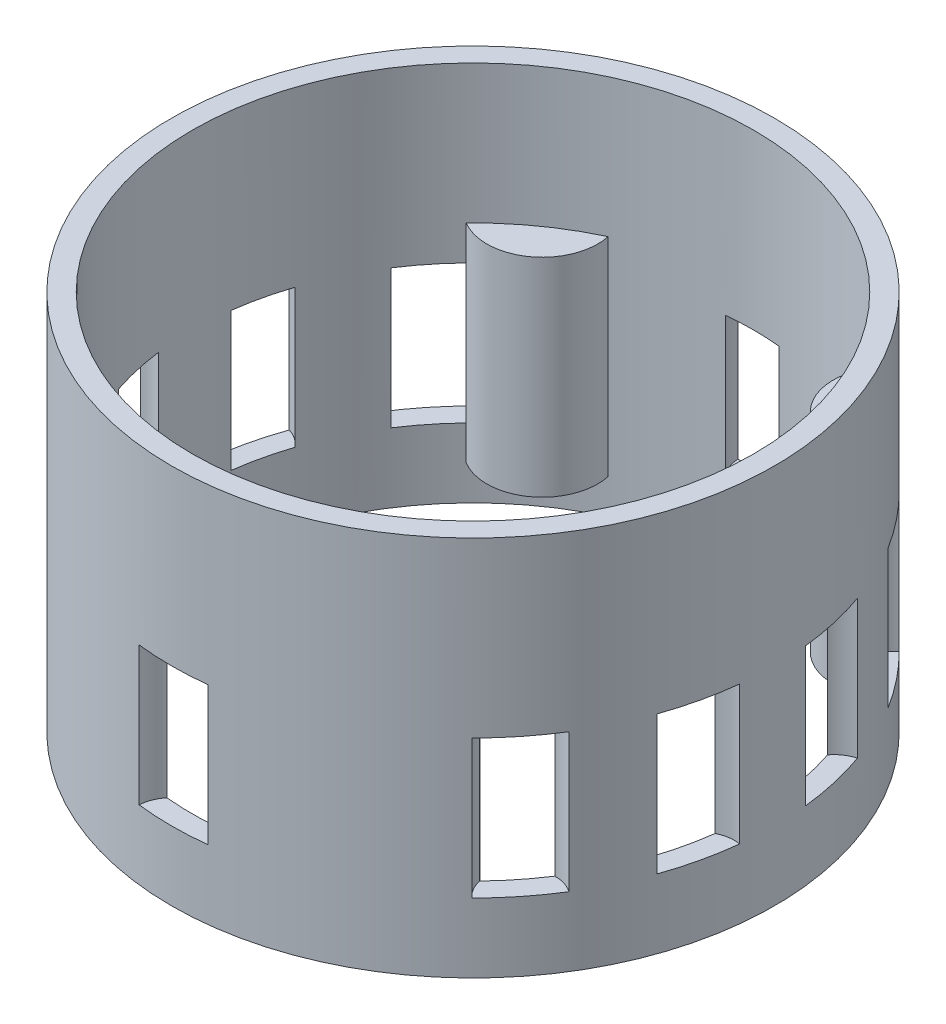
SolidWorks part; units mm, degrees
ref_plane "Front Plane" through (0, 0, 0) normal (0, 0, 1) x (1, 0, 0)
ref_plane "Top Plane" through (0, 0, 0) normal (0, 1, 0) x (1, 0, 0)
ref_plane "Right Plane" through (0, 0, 0) normal (1, 0, 0) x (0, 0, -1)
sketch "Sketch1" plane through (0, 0, 0) normal (0, 1, 0) x (1, 0, 0)
  line L1 (-25, 35) -> (25, 35) construction
  line L2 (-25, 35) -> (-25, -35) construction
  line L3 (-25, -35) -> (25, -35) construction
  line L4 (25, 35) -> (25, -35) construction
  line L5 (-25, 35) -> (25, -35) construction
  line L6 (-25, -35) -> (25, 35) construction
  circle A0 centre (0, 0) radius 40.5
  circle A1 centre (0, 0) radius 43.5
  arc A2 (-29.123, 28.1443) -> (-17.1777, 36.6767) centre (-25, 35) ccw
  arc A3 (17.1777, 36.6767) -> (29.123, 28.1443) centre (25, 35) ccw
  arc A4 (29.123, -28.1443) -> (17.1777, -36.6767) centre (25, -35) ccw
  arc A5 (-17.1777, -36.6767) -> (-29.123, -28.1443) centre (-25, -35) ccw
  dimension "D1" = 81
  dimension "D2" = 87
  dimension "D5" = 16
  dimension "D3" = 70
  dimension "D4" = 50
extrude "Boss-Extrude1" add sketch "Sketch1" along normal blind 30 contours A1 A0 | A0 A2 | A0 A5 | A0 A4 | A0 A3
sketch "Sketch2" plane through (0, 30, 0) normal (0, 1, 0) x (1, 0, 0)
  circle A0 centre (0, 0) radius 43.5
  circle A1 centre (0, 0) radius 40.5
extrude "Boss-Extrude2" add sketch "Sketch2" along normal blind 20
sketch "Sketch3" plane through (0, 0, 0) normal (0, -1, 0) x (1, 0, 0)
  circle A0 centre (0, 0) radius 43.5
  circle A1 centre (0, 0) radius 40.5
extrude "Boss-Extrude3" add sketch "Sketch3" along normal blind 5
ref_plane "Plane1" through (0, 15, 0) normal (0, 1, 0) x (1, 0, 0)
sketch "Sketch4" plane through (0, 0, 0) normal (0, 1, 0) x (1, 0, 0)
  line L0 (0, 0) -> (3.8552, 40.3161) construction
  line L1 (0, 0) -> (20.9659, 34.6508) construction
  circle A0 centre (0, 0) radius 40.5 construction
  circle A1 centre (0, 0) radius 43.5 construction
  arc A2 (3.8552, 40.3161) -> (-3.8552, 40.3161) centre (0, 0) ccw
  arc A3 (4.9917, 43.2126) -> (-4.9917, 43.2126) centre (0, 0) ccw
  arc A4 (3.8552, 40.3161) -> (4.9917, 43.2126) centre (0, 43.5) ccw
  arc A5 (-4.9917, 43.2126) -> (-3.8552, 40.3161) centre (0, 43.5) ccw
  arc A10 (33.9241, 22.1225) -> (29.1167, 28.1508) centre (0, 0) ccw
  arc A11 (30.6727, 30.8453) -> (29.1167, 28.1508) centre (34.0097, 27.1218) ccw
  arc A12 (36.8973, 23.0399) -> (30.6727, 30.8453) centre (0, 0) ccw
  arc A13 (33.9241, 22.1225) -> (36.8973, 23.0399) centre (34.0097, 27.1218) ccw
  arc A14 (40.1632, 5.2126) -> (38.4474, 12.7297) centre (0, 0) ccw
  arc A15 (41.0184, 14.4823) -> (38.4474, 12.7297) centre (42.4094, 9.6797) ccw
  arc A16 (43.24, 4.7491) -> (41.0184, 14.4823) centre (0, 0) ccw
  arc A17 (40.1632, 5.2126) -> (43.24, 4.7491) centre (42.4094, 9.6797) ccw
  arc A18 (38.4474, -12.7297) -> (40.1632, -5.2126) centre (0, 0) ccw
  arc A19 (43.24, -4.7491) -> (40.1632, -5.2126) centre (42.4094, -9.6797) ccw
  arc A20 (41.0184, -14.4823) -> (43.24, -4.7491) centre (0, 0) ccw
  arc A21 (38.4474, -12.7297) -> (41.0184, -14.4823) centre (42.4094, -9.6797) ccw
  arc A22 (29.1167, -28.1508) -> (33.9241, -22.1225) centre (0, 0) ccw
  arc A23 (36.8973, -23.0399) -> (33.9241, -22.1225) centre (34.0097, -27.1218) ccw
  arc A24 (30.6727, -30.8453) -> (36.8973, -23.0399) centre (0, 0) ccw
  arc A25 (29.1167, -28.1508) -> (30.6727, -30.8453) centre (34.0097, -27.1218) ccw
  arc A30 (-3.8552, -40.3161) -> (3.8552, -40.3161) centre (0, 0) ccw
  arc A31 (4.9917, -43.2126) -> (3.8552, -40.3161) centre (0, -43.5) ccw
  arc A32 (-4.9917, -43.2126) -> (4.9917, -43.2126) centre (0, 0) ccw
  arc A33 (-3.8552, -40.3161) -> (-4.9917, -43.2126) centre (0, -43.5) ccw
  arc A38 (-33.9241, -22.1225) -> (-29.1167, -28.1508) centre (0, 0) ccw
  arc A39 (-30.6727, -30.8453) -> (-29.1167, -28.1508) centre (-34.0097, -27.1218) ccw
  arc A40 (-36.8973, -23.0399) -> (-30.6727, -30.8453) centre (0, 0) ccw
  arc A41 (-33.9241, -22.1225) -> (-36.8973, -23.0399) centre (-34.0097, -27.1218) ccw
  arc A42 (-40.1632, -5.2126) -> (-38.4474, -12.7297) centre (0, 0) ccw
  arc A43 (-41.0184, -14.4823) -> (-38.4474, -12.7297) centre (-42.4094, -9.6797) ccw
  arc A44 (-43.24, -4.7491) -> (-41.0184, -14.4823) centre (0, 0) ccw
  arc A45 (-40.1632, -5.2126) -> (-43.24, -4.7491) centre (-42.4094, -9.6797) ccw
  arc A46 (-38.4474, 12.7297) -> (-40.1632, 5.2126) centre (0, 0) ccw
  arc A47 (-43.24, 4.7491) -> (-40.1632, 5.2126) centre (-42.4094, 9.6797) ccw
  arc A48 (-41.0184, 14.4823) -> (-43.24, 4.7491) centre (0, 0) ccw
  arc A49 (-38.4474, 12.7297) -> (-41.0184, 14.4823) centre (-42.4094, 9.6797) ccw
  arc A50 (-29.1167, 28.1508) -> (-33.9241, 22.1225) centre (0, 0) ccw
  arc A51 (-36.8973, 23.0399) -> (-33.9241, 22.1225) centre (-34.0097, 27.1218) ccw
  arc A52 (-30.6727, 30.8453) -> (-36.8973, 23.0399) centre (0, 0) ccw
  arc A53 (-29.1167, 28.1508) -> (-30.6727, 30.8453) centre (-34.0097, 27.1218) ccw
  arc A58 (-14.0191, 37.9963) -> (-14.2519, 41.0991) centre (-18.8739, 39.1921) ccw
  arc A59 (-23.2467, 36.7674) -> (-20.9659, 34.6508) centre (-18.8739, 39.1921) ccw
  arc A60 (-14.2519, 41.0991) -> (-23.2467, 36.7674) centre (0, 0) ccw
  arc A61 (-14.0191, 37.9963) -> (-20.9659, 34.6508) centre (0, 0) ccw
  arc A62 (20.9659, 34.6508) -> (14.0191, 37.9963) centre (0, 0) ccw
  arc A63 (23.2467, 36.7674) -> (14.2519, 41.0991) centre (0, 0) ccw
  arc A64 (14.2519, 41.0991) -> (14.0191, 37.9963) centre (18.8739, 39.1921) ccw
  arc A65 (20.9659, 34.6508) -> (23.2467, 36.7674) centre (18.8739, 39.1921) ccw
  arc A66 (23.2467, -36.7674) -> (20.9659, -34.6508) centre (18.8739, -39.1921) ccw
  arc A67 (14.0191, -37.9963) -> (20.9659, -34.6508) centre (0, 0) ccw
  arc A68 (14.0191, -37.9963) -> (14.2519, -41.0991) centre (18.8739, -39.1921) ccw
  arc A69 (14.2519, -41.0991) -> (23.2467, -36.7674) centre (0, 0) ccw
  arc A70 (-20.9659, -34.6508) -> (-23.2467, -36.7674) centre (-18.8739, -39.1921) ccw
  arc A71 (-14.2519, -41.0991) -> (-14.0191, -37.9963) centre (-18.8739, -39.1921) ccw
  arc A72 (-20.9659, -34.6508) -> (-14.0191, -37.9963) centre (0, 0) ccw
  arc A73 (-23.2467, -36.7674) -> (-14.2519, -41.0991) centre (0, 0) ccw
  dimension "D1" = 10
  dimension "D3" = 25.714
  dimension "D2" = 14
sketch "Sketch5" plane through (0, 15, 0) normal (0, 1, 0) x (1, 0, 0)
  arc A0 (-4.9917, 43.2126) -> (-3.8552, 40.3161) centre (0, 43.5) ccw construction
  arc A1 (4.9917, 43.2126) -> (-4.9917, 43.2126) centre (0, 0) ccw construction
  arc A2 (3.8552, 40.3161) -> (4.9917, 43.2126) centre (0, 43.5) ccw construction
  arc A3 (3.8552, 40.3161) -> (-3.8552, 40.3161) centre (0, 0) ccw construction
  arc A4 (33.9241, 22.1225) -> (29.1167, 28.1508) centre (0, 0) ccw construction
  arc A5 (30.6727, 30.8453) -> (29.1167, 28.1508) centre (34.0097, 27.1218) ccw construction
  arc A6 (36.8973, 23.0399) -> (30.6727, 30.8453) centre (0, 0) ccw construction
  arc A7 (33.9241, 22.1225) -> (36.8973, 23.0399) centre (34.0097, 27.1218) ccw construction
  arc A8 (40.1632, 5.2126) -> (38.4474, 12.7297) centre (0, 0) ccw construction
  arc A9 (41.0184, 14.4823) -> (38.4474, 12.7297) centre (42.4094, 9.6797) ccw construction
  arc A10 (43.24, 4.7491) -> (41.0184, 14.4823) centre (0, 0) ccw construction
  arc A11 (40.1632, 5.2126) -> (43.24, 4.7491) centre (42.4094, 9.6797) ccw construction
  arc A12 (41.0184, -14.4823) -> (43.24, -4.7491) centre (0, 0) ccw construction
  arc A13 (38.4474, -12.7297) -> (40.1632, -5.2126) centre (0, 0) ccw construction
  arc A14 (43.24, -4.7491) -> (40.1632, -5.2126) centre (42.4094, -9.6797) ccw construction
  arc A15 (38.4474, -12.7297) -> (41.0184, -14.4823) centre (42.4094, -9.6797) ccw construction
  arc A16 (29.1167, -28.1508) -> (30.6727, -30.8453) centre (34.0097, -27.1218) ccw construction
  arc A17 (30.6727, -30.8453) -> (36.8973, -23.0399) centre (0, 0) ccw construction
  arc A18 (29.1167, -28.1508) -> (33.9241, -22.1225) centre (0, 0) ccw construction
  arc A19 (36.8973, -23.0399) -> (33.9241, -22.1225) centre (34.0097, -27.1218) ccw construction
  arc A20 (4.9917, -43.2126) -> (3.8552, -40.3161) centre (0, -43.5) ccw construction
  arc A21 (-4.9917, -43.2126) -> (4.9917, -43.2126) centre (0, 0) ccw construction
  arc A22 (-3.8552, -40.3161) -> (3.8552, -40.3161) centre (0, 0) ccw construction
  arc A23 (-3.8552, -40.3161) -> (-4.9917, -43.2126) centre (0, -43.5) ccw construction
  arc A24 (-36.8973, -23.0399) -> (-30.6727, -30.8453) centre (0, 0) ccw construction
  arc A25 (-30.6727, -30.8453) -> (-29.1167, -28.1508) centre (-34.0097, -27.1218) ccw construction
  arc A26 (-33.9241, -22.1225) -> (-29.1167, -28.1508) centre (0, 0) ccw construction
  arc A27 (-33.9241, -22.1225) -> (-36.8973, -23.0399) centre (-34.0097, -27.1218) ccw construction
  arc A28 (-43.24, -4.7491) -> (-41.0184, -14.4823) centre (0, 0) ccw construction
  arc A29 (-40.1632, -5.2126) -> (-43.24, -4.7491) centre (-42.4094, -9.6797) ccw construction
  arc A30 (-40.1632, -5.2126) -> (-38.4474, -12.7297) centre (0, 0) ccw construction
  arc A31 (-41.0184, -14.4823) -> (-38.4474, -12.7297) centre (-42.4094, -9.6797) ccw construction
  arc A32 (-38.4474, 12.7297) -> (-40.1632, 5.2126) centre (0, 0) ccw construction
  arc A33 (-38.4474, 12.7297) -> (-41.0184, 14.4823) centre (-42.4094, 9.6797) ccw construction
  arc A34 (-41.0184, 14.4823) -> (-43.24, 4.7491) centre (0, 0) ccw construction
  arc A35 (-43.24, 4.7491) -> (-40.1632, 5.2126) centre (-42.4094, 9.6797) ccw construction
  arc A36 (-29.1167, 28.1508) -> (-30.6727, 30.8453) centre (-34.0097, 27.1218) ccw construction
  arc A37 (-29.1167, 28.1508) -> (-33.9241, 22.1225) centre (0, 0) ccw construction
  arc A38 (-30.6727, 30.8453) -> (-36.8973, 23.0399) centre (0, 0) ccw construction
  arc A39 (-36.8973, 23.0399) -> (-33.9241, 22.1225) centre (-34.0097, 27.1218) ccw construction
  arc A40 (-4.9917, 43.2126) -> (-3.8552, 40.3161) centre (0, 43.5) ccw
  arc A41 (4.9917, 43.2126) -> (-4.9917, 43.2126) centre (0, 0) ccw
  arc A42 (3.8552, 40.3161) -> (4.9917, 43.2126) centre (0, 43.5) ccw
  arc A43 (3.8552, 40.3161) -> (-3.8552, 40.3161) centre (0, 0) ccw
  arc A44 (33.9241, 22.1225) -> (29.1167, 28.1508) centre (0, 0) ccw
  arc A45 (30.6727, 30.8453) -> (29.1167, 28.1508) centre (34.0097, 27.1218) ccw
  arc A46 (36.8973, 23.0399) -> (30.6727, 30.8453) centre (0, 0) ccw
  arc A47 (33.9241, 22.1225) -> (36.8973, 23.0399) centre (34.0097, 27.1218) ccw
  arc A48 (40.1632, 5.2126) -> (38.4474, 12.7297) centre (0, 0) ccw
  arc A49 (41.0184, 14.4823) -> (38.4474, 12.7297) centre (42.4094, 9.6797) ccw
  arc A50 (43.24, 4.7491) -> (41.0184, 14.4823) centre (0, 0) ccw
  arc A51 (40.1632, 5.2126) -> (43.24, 4.7491) centre (42.4094, 9.6797) ccw
  arc A52 (41.0184, -14.4823) -> (43.24, -4.7491) centre (0, 0) ccw
  arc A53 (38.4474, -12.7297) -> (40.1632, -5.2126) centre (0, 0) ccw
  arc A54 (43.24, -4.7491) -> (40.1632, -5.2126) centre (42.4094, -9.6797) ccw
  arc A55 (38.4474, -12.7297) -> (41.0184, -14.4823) centre (42.4094, -9.6797) ccw
  arc A56 (29.1167, -28.1508) -> (30.6727, -30.8453) centre (34.0097, -27.1218) ccw
  arc A57 (30.6727, -30.8453) -> (36.8973, -23.0399) centre (0, 0) ccw
  arc A58 (29.1167, -28.1508) -> (33.9241, -22.1225) centre (0, 0) ccw
  arc A59 (36.8973, -23.0399) -> (33.9241, -22.1225) centre (34.0097, -27.1218) ccw
  arc A60 (4.9917, -43.2126) -> (3.8552, -40.3161) centre (0, -43.5) ccw
  arc A61 (-4.9917, -43.2126) -> (4.9917, -43.2126) centre (0, 0) ccw
  arc A62 (-3.8552, -40.3161) -> (3.8552, -40.3161) centre (0, 0) ccw
  arc A63 (-3.8552, -40.3161) -> (-4.9917, -43.2126) centre (0, -43.5) ccw
  arc A64 (-36.8973, -23.0399) -> (-30.6727, -30.8453) centre (0, 0) ccw
  arc A65 (-30.6727, -30.8453) -> (-29.1167, -28.1508) centre (-34.0097, -27.1218) ccw
  arc A66 (-33.9241, -22.1225) -> (-29.1167, -28.1508) centre (0, 0) ccw
  arc A67 (-33.9241, -22.1225) -> (-36.8973, -23.0399) centre (-34.0097, -27.1218) ccw
  arc A68 (-43.24, -4.7491) -> (-41.0184, -14.4823) centre (0, 0) ccw
  arc A69 (-40.1632, -5.2126) -> (-43.24, -4.7491) centre (-42.4094, -9.6797) ccw
  arc A70 (-40.1632, -5.2126) -> (-38.4474, -12.7297) centre (0, 0) ccw
  arc A71 (-41.0184, -14.4823) -> (-38.4474, -12.7297) centre (-42.4094, -9.6797) ccw
  arc A72 (-38.4474, 12.7297) -> (-40.1632, 5.2126) centre (0, 0) ccw
  arc A73 (-38.4474, 12.7297) -> (-41.0184, 14.4823) centre (-42.4094, 9.6797) ccw
  arc A74 (-41.0184, 14.4823) -> (-43.24, 4.7491) centre (0, 0) ccw
  arc A75 (-43.24, 4.7491) -> (-40.1632, 5.2126) centre (-42.4094, 9.6797) ccw
  arc A76 (-29.1167, 28.1508) -> (-30.6727, 30.8453) centre (-34.0097, 27.1218) ccw
  arc A77 (-29.1167, 28.1508) -> (-33.9241, 22.1225) centre (0, 0) ccw
  arc A78 (-30.6727, 30.8453) -> (-36.8973, 23.0399) centre (0, 0) ccw
  arc A79 (-36.8973, 23.0399) -> (-33.9241, 22.1225) centre (-34.0097, 27.1218) ccw
extrude "Cut-Extrude1" cut sketch "Sketch5" against normal blind 10 and the other way blind 10
